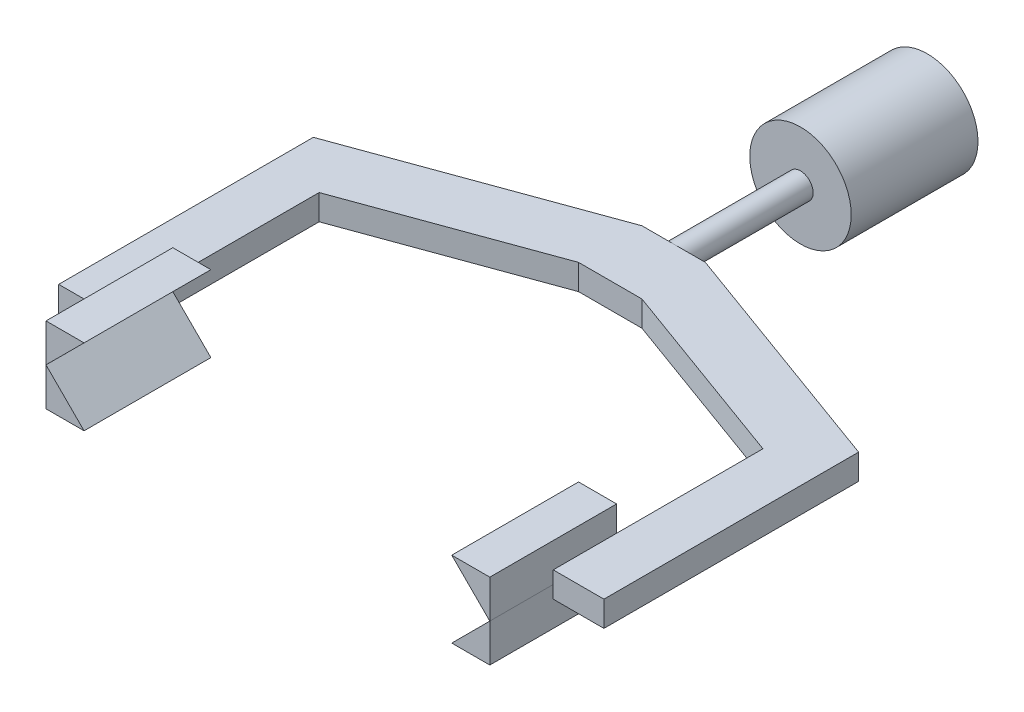
SolidWorks part; units mm, degrees
ref_plane "Front Plane" through (0, 0, 0) normal (0, 0, 1) x (1, 0, 0)
ref_plane "Top Plane" through (0, 0, 0) normal (0, 1, 0) x (1, 0, 0)
ref_plane "Right Plane" through (0, 0, 0) normal (1, 0, 0) x (0, 0, -1)
sketch "Sketch1" plane through (0, 0, 0) normal (0, 0, 1) x (1, 0, 0)
  circle A0 centre (0, 0) radius 4
  dimension "D1" = 8
extrude "Boss-Extrude1" add sketch "Sketch1" along normal blind 10
sketch "Sketch2" plane through (0, 0, 10) normal (0, 0, 1) x (1, 0, 0)
  circle A0 centre (0, 0) radius 1
  dimension "D1" = 2
extrude "Boss-Extrude2" add sketch "Sketch2" along normal blind 10
sketch "Sketch3" plane through (0, 0, 0) normal (0, 1, 0) x (1, 0, 0)
  line L0 (-1, -20) -> (1, -20) construction
  line L1 (-2.5, -20) -> (2.5, -20)
  line L2 (-2.5, -20) -> (-2.5, -25)
  line L3 (-2.5, -25) -> (2.5, -25)
  line L4 (2.5, -20) -> (2.5, -25)
  line L5 (-1, -20) -> (1, -20) construction
  point P9 (1, -20)
  point P10 (0, -20)
  point P12 (0, -20)
  dimension "D1" = 5
  dimension "D2" = 5
extrude "Boss-Extrude3" add sketch "Sketch3" along normal mid plane 2
sketch "Sketch5" plane through (0, 0, 0) normal (0, 1, 0) x (1, 0, 0)
  line L0 (2.5, -20) -> (21.5, -26.9154)
  line L1 (21.5, -26.9154) -> (21.5, -47)
  line L2 (21.5, -47) -> (17.5, -47)
  line L3 (17.5, -47) -> (17.5, -30.4596)
  line L4 (17.5, -30.4596) -> (2.5, -25)
  line L5 (2.5, -25) -> (2.5, -20) construction
  line L6 (-2.5, -25) -> (2.5, -25) construction
  line L7 (0, -20) -> (0, -52.6055) construction
  line L8 (2.5, -20) -> (2.5, -25)
  dimension "D1" = 70
  dimension "D2" = 15
  dimension "D3" = 4
  dimension "D4" = 22
extrude "Boss-Extrude4" add sketch "Sketch5" along normal mid plane 2
mirror "Mirror1" about plane through (0, 0, 0) normal (1, 0, 0) of "Boss-Extrude4"
sketch "Sketch6" plane through (0, 0, 47) normal (0, 0, 1) x (1, 0, 0)
  line L0 (17.5, 0) -> (14.4972, 3.0028)
  line L1 (17.5, 1) -> (17.5, -1) construction
  line L2 (14.4972, 3.0028) -> (17.5, 3.0028)
  line L3 (17.5, 3.0028) -> (17.5, 0.0028)
  line L4 (23.65, 0) -> (-23.65, 0) construction
  line L5 (17.5, -3.0028) -> (17.5, -0.0028)
  line L6 (17.5, 0) -> (14.4972, -3.0028)
  line L7 (14.4972, -3.0028) -> (17.5, -3.0028)
  line L8 (2.5, -1) -> (17.5, -1)
  line L9 (-17.5, 0.0028) -> (-14.4972, 3.0028)
  line L10 (17.5, -1) -> (17.5, 1)
  line L11 (17.5, 1) -> (2.5, 1)
  line L12 (2.5, 1) -> (2.5, -1)
  line L14 (17.5, 0) -> (17.5, 0.0028)
  line L17 (0, -4.4) -> (0, 4.4) construction
  line L18 (-17.5, 0) -> (-14.4972, -3.0028)
  line L19 (-17.5, 3.0028) -> (-17.5, 0.0028)
  line L21 (-14.4972, 3.0028) -> (-17.5, 3.0028)
  line L22 (-14.4972, -3.0028) -> (-17.5, -3.0028)
  line L23 (-17.5, -3.0028) -> (-17.5, 0)
  line M9 (17.5, 1) -> (17.5, -1)
  dimension "D1" = 3.0028
  dimension "D2" = 3.0028
  dimension "D3" = 45
  dimension "D4" = 3
  dimension "D5" = 0
extrude "Boss-Extrude7" add sketch "Sketch6" along normal mid plane 10 separate body contours L3 L2 L0 M9 | L6 L7 L5 M9 | L23 L22 L18 | L9 L21 L19
